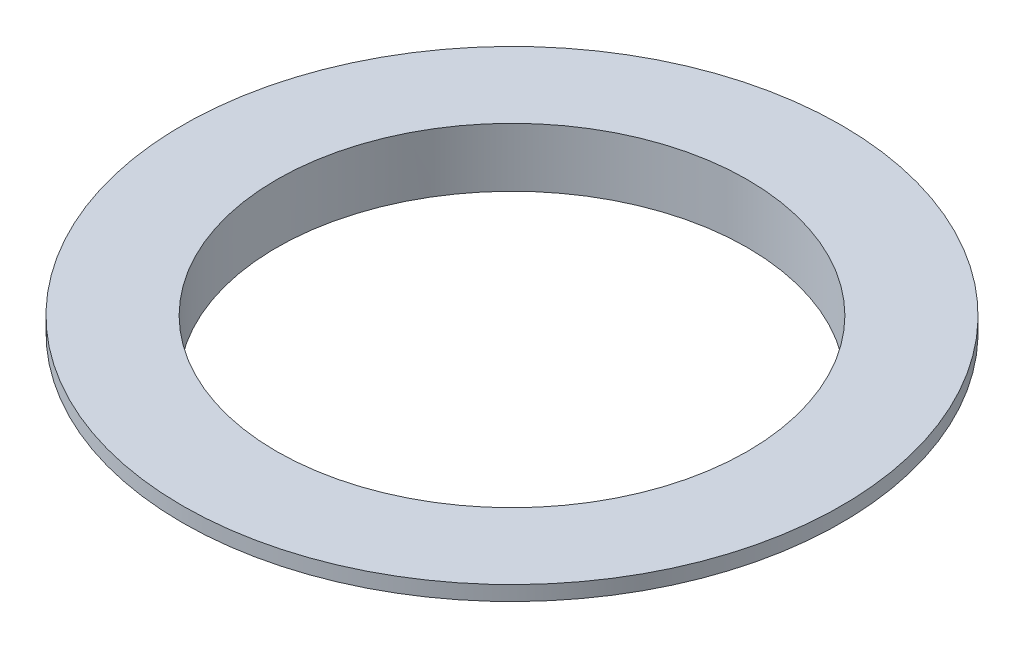
SolidWorks part; units mm, degrees
material "PVC Rigid"
ref_plane "Front Plane" through (0, 0, 0) normal (0, 0, 1) x (1, 0, 0)
ref_plane "Top Plane" through (0, 0, 0) normal (0, 1, 0) x (1, 0, 0)
ref_plane "Right Plane" through (0, 0, 0) normal (1, 0, 0) x (0, 0, -1)
sketch "Sketch1" plane through (0, 0, 0) normal (1, 0, 0) x (0, 0, -1)
  line L0 (50.8, 0) -> (57.15, 0)
  line L1 (57.15, 0) -> (57.15, 9.525)
  line L2 (57.15, 9.525) -> (71.12, 9.525)
  line L3 (71.12, 9.525) -> (71.12, 12.7)
  line L4 (71.12, 12.7) -> (0, 12.7)
  line L5 (0, 12.7) -> (0, 9.525)
  line L6 (0, 9.525) -> (50.8, 9.525)
  line L7 (50.8, 9.525) -> (50.8, 0)
  line L8 (0, 0) -> (0, 12.7) construction
  dimension "D1" = 12.7
  dimension "D2" = 3.175
  dimension "D3" = 57.15
  dimension "D4" = 71.12
  dimension "D5" = 50.8
  dimension "D6" = 12.7
revolve "Revolve1" add sketch "Sketch1" angle 360 about L8
sketch "Sketch4" plane through (0, 12.7, 0) normal (0, 1, 0) x (1, 0, 0)
  circle A0 centre (0, 0) radius 50.8
  dimension "D1" = 101.6
extrude "Cut-Extrude1" cut sketch "Sketch4" against normal through all
